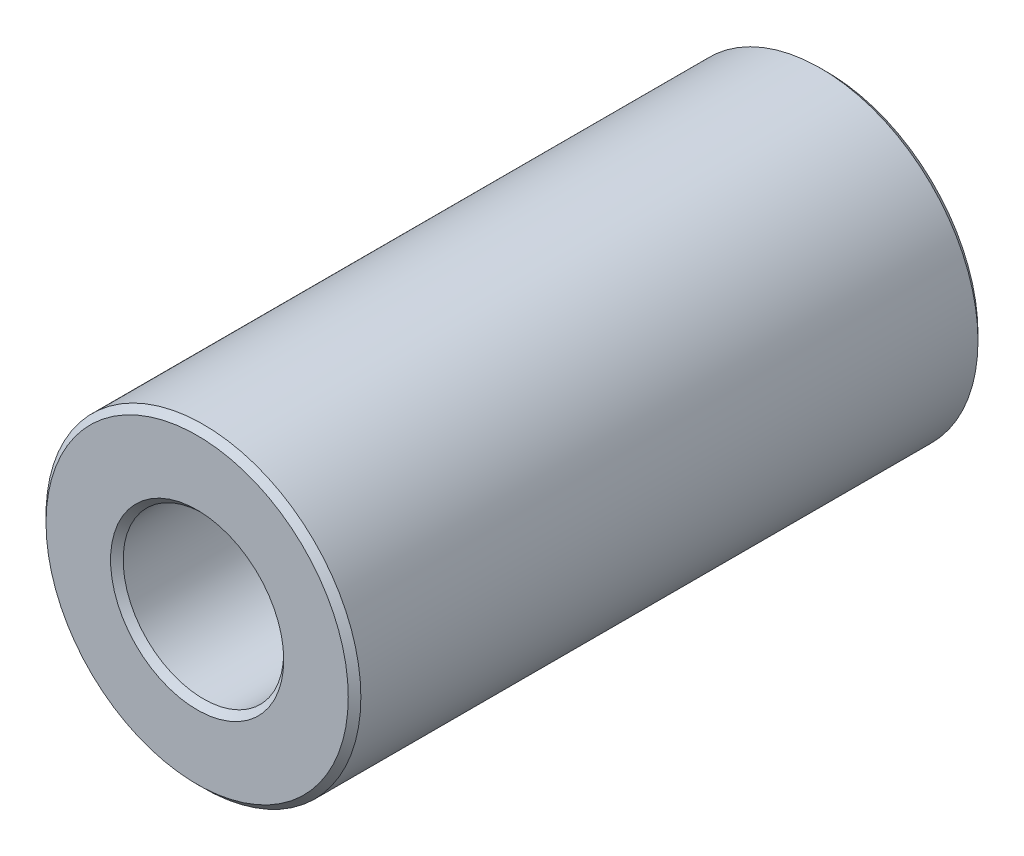
SolidWorks part; units mm, degrees
material "6061-T6 (SS)"
ref_plane "Front Plane" through (0, 0, 0) normal (0, 0, 1) x (1, 0, 0)
ref_plane "Top Plane" through (0, 0, 0) normal (0, 1, 0) x (1, 0, 0)
ref_plane "Right Plane" through (0, 0, 0) normal (1, 0, 0) x (0, 0, -1)
sketch "Sketch1" plane through (0, 0, 0) normal (0, 0, 1) x (1, 0, 0)
  circle A0 centre (0, 0) radius 2.55
  circle A1 centre (0, 0) radius 5
  dimension "D1" = 5.1
  dimension "D2" = 10
extrude "Boss-Extrude1" add sketch "Sketch1" along normal blind 20
chamfer "Chamfer1" distance 0.2 angle 45 4 edges at (5, 0, 0) (2.55, 0, 0) (2.55, 0, 20) (5, 0, 20)
